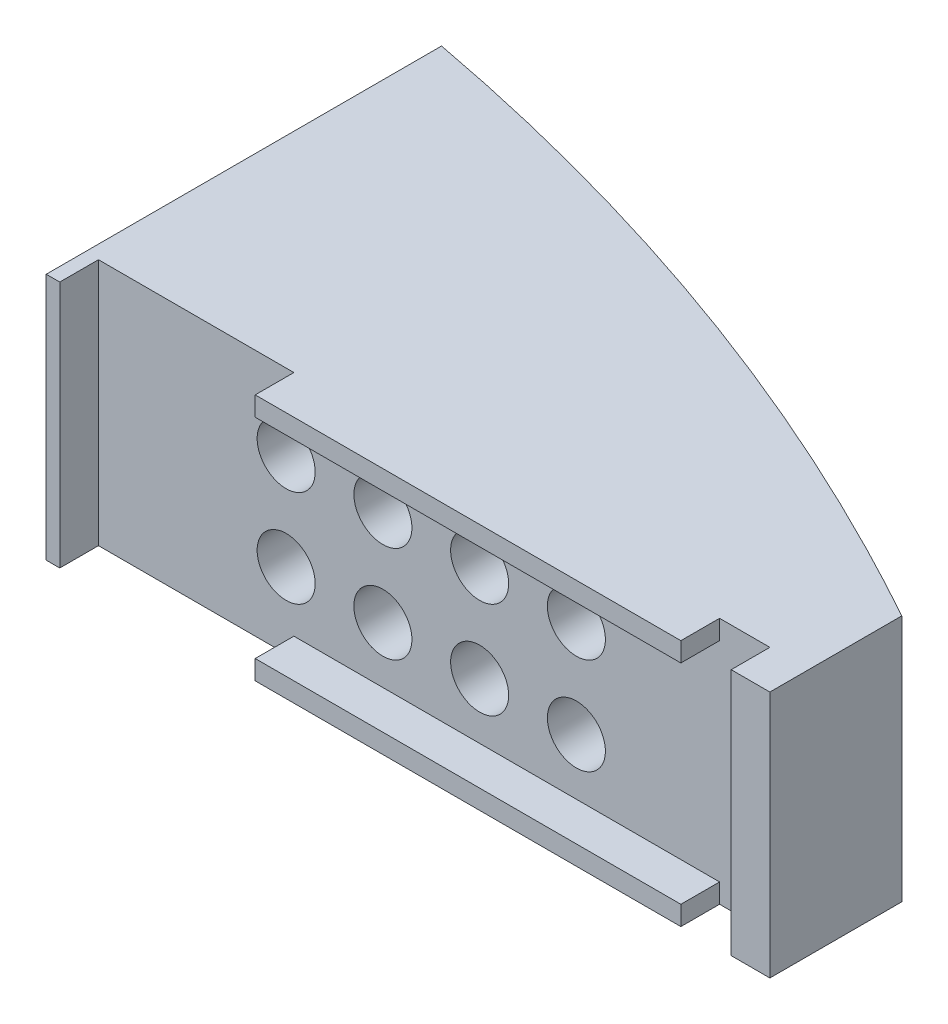
SolidWorks part; units mm, degrees
ref_plane "Front Plane" through (0, 0, 0) normal (0, 0, 1) x (1, 0, 0)
ref_plane "Top Plane" through (0, 0, 0) normal (0, 1, 0) x (1, 0, 0)
ref_plane "Right Plane" through (0, 0, 0) normal (1, 0, 0) x (0, 0, -1)
sketch "Sketch1" plane through (0, 0, 0) normal (0, 1, 0) x (1, 0, 0)
  line L0 (0, 15) -> (0, 0)
  line L1 (0, 0) -> (18.85, 0)
  line L2 (18.85, 0) -> (18.85, 10)
  line L3 (18.85, 10) -> (0, 15)
  dimension "D2" = 15
  dimension "D3" = 10
extrude "Boss-Extrude1" add sketch "Sketch1" along normal blind 6.4
sketch "Sketch2" plane through (0, 0, 0) normal (0, 0, 1) x (1, 0, 0)
  line L0 (0, 3.2) -> (18.85, 3.2) construction
  line L1 (0, 6.4) -> (0, 0) construction
  line L2 (18.85, 6.4) -> (18.85, 0) construction
  line L4 (5.35, 4.45) -> (12.85, 4.45) construction
  line L5 (5.35, 4.45) -> (5.35, 1.95) construction
  line L6 (5.35, 1.95) -> (12.85, 1.95) construction
  line L7 (12.85, 4.45) -> (12.85, 1.95) construction
  line L8 (5.35, 4.45) -> (12.85, 1.95) construction
  line L9 (5.35, 1.95) -> (12.85, 4.45) construction
  circle A0 centre (12.85, 4.45) radius 0.75
  circle A1 centre (12.85, 1.95) radius 0.75
  circle A2 centre (5.35, 1.95) radius 0.75
  circle A3 centre (5.35, 4.45) radius 0.75
  circle A4 centre (7.85, 4.45) radius 0.75
  circle A5 centre (10.35, 4.45) radius 0.75
  circle A6 centre (7.85, 1.95) radius 0.75
  circle A7 centre (10.35, 1.95) radius 0.75
  point P8 (9.1, 3.2)
  dimension "D1" = 1.5
  dimension "D3" = 2.5
  dimension "D4" = 2.5
  dimension "D5" = 2.5
  dimension "D6" = 2.5
  dimension "D2" = 7.5
  dimension "D7" = 2.5
  dimension "D8" = 6
extrude "Cut-Extrude1" cut sketch "Sketch2" against normal up to next
sketch "Sketch3" plane through (0, 6.4, 0) normal (0, 1, 0) x (1, 0, 0)
  line L0 (0, 15) -> (0, 0) construction
  line L1 (0, 15) -> (0, 9.2429)
  line L2 (18.85, 10) -> (0, 15) construction
  line L3 (18.85, 10) -> (0, 15)
  line L4 (18.85, 0) -> (18.85, 10) construction
  line L5 (18.85, 2.4084) -> (18.85, 10)
  ellipse E1 centre (-7.8364, -62.6858) end of major axis (4.8664, -134.7272) minor radius 64.5447 (18.85, 2.4084) -> (0, 9.2429) ccw
  ellipse E2 centre (-22.117, -54.3027) end of major axis (-95.4781, -69.896) minor radius 65 (0.15, 9.2097) -> (18.85, 2.4084) ccw construction
extrude "Cut-Extrude2" cut sketch "Sketch3" against normal up to next
sketch "Sketch9" plane through (0, 0, 0) normal (0, 0, 1) x (1, 0, 0)
  line L0 (0, 0) -> (18.85, 0) construction
  line L1 (0, 6.4) -> (0.5, 6.4)
  line L2 (0, 6.4) -> (0, 0)
  line L3 (0, 0) -> (0.5, 0)
  line L4 (0.5, 6.4) -> (0.5, 0)
  line L5 (0, 6.4) -> (18.85, 6.4) construction
  line L6 (18.85, 6.4) -> (17.85, 6.4)
  line L7 (18.85, 6.4) -> (18.85, 0)
  line L8 (18.85, 0) -> (17.85, 0)
  line L9 (17.85, 6.4) -> (17.85, 0)
  line L10 (5.55, 6.4) -> (16.55, 6.4)
  line L11 (5.55, 6.4) -> (5.55, 5.9)
  line L12 (5.55, 5.9) -> (16.55, 5.9)
  line L13 (16.55, 6.4) -> (16.55, 5.9)
  line L15 (5.55, 0) -> (16.55, 0)
  line L16 (5.55, 0) -> (5.55, 0.5)
  line L17 (5.55, 0.5) -> (16.55, 0.5)
  line L18 (16.55, 0) -> (16.55, 0.5)
  dimension "D1" = 0.5
  dimension "D2" = 1
  dimension "D3" = 2.3
  dimension "D4" = 11
  dimension "D5" = 0.5
extrude "Boss-Extrude2" add sketch "Sketch9" along normal blind 1
sketch "Sketch10" plane through (0, 0, 0) normal (-1, 0, 0) x (0, 0, 1)
  line L4 (1, 6.4) -> (-9.2429, 6.4)
  line L5 (-9.2429, 6.4) -> (-9.2429, 0)
  line L6 (-9.2429, 0) -> (1, 0)
  line L7 (1, 0) -> (1, 6.4)
  line L8 (1, 6.4) -> (-9.2429, 6.4)
  line L9 (-9.2429, 6.4) -> (-9.2429, 0)
  line L10 (-9.2429, 0) -> (1, 0)
  line L13 (1, 0) -> (1, 6.4)
  dimension "D1" = 0
extrude "Cut-Extrude7" cut sketch "Sketch10" against normal blind 0.15
